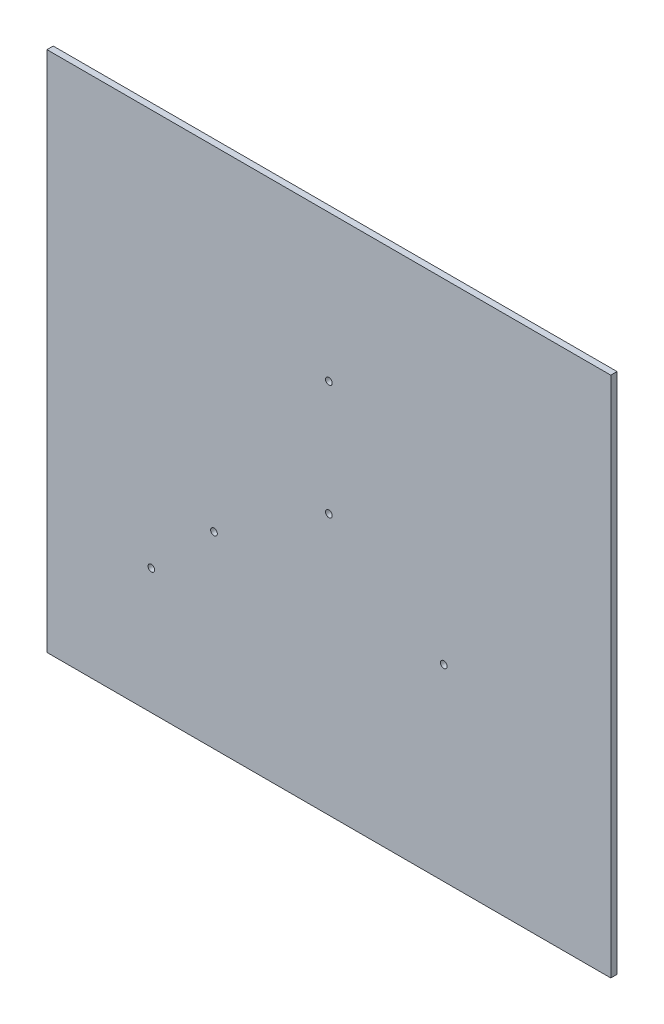
SolidWorks part; units mm, degrees
ref_plane "正面" through (0, 0, 0) normal (0, 0, 1) x (1, 0, 0)
ref_plane "平面" through (0, 0, 0) normal (0, 1, 0) x (1, 0, 0)
ref_plane "右側面" through (0, 0, 0) normal (1, 0, 0) x (0, 0, -1)
sketch "ｽｹｯﾁ1" plane through (0, 0, 0) normal (0, 0, 1) x (1, 0, 0)
  line L0 (-55, -35) -> (55, -35) construction
  line L1 (-135, -125) -> (135, -125)
  line L2 (-135, -125) -> (-135, 125)
  line L3 (-135, 125) -> (135, 125)
  line L4 (135, -125) -> (135, 125)
  line L5 (-135, -125) -> (135, 125) construction
  line L6 (-135, 125) -> (135, -125) construction
  line L7 (0, -1.65) -> (0, 1.65) construction
  circle A0 centre (-85, -65) radius 1.6
  circle A1 centre (0, 55) radius 1.6
  circle A2 centre (-55, -35) radius 1.6
  circle A3 centre (55, -35) radius 1.6
  circle A4 centre (0, 0) radius 1.6
  point P0 (0, 0)
  point P14 (0, -35)
  dimension "D3" = 80
  dimension "D5" = 180
  dimension "D6" = 60
  dimension "D7" = 50
  dimension "D8" = 3.2
  dimension "D1" = 250
  dimension "D2" = 270
  dimension "D4" = 90
extrude "ﾎﾞｽ - 押し出し1" add sketch "ｽｹｯﾁ1" along normal blind 3
